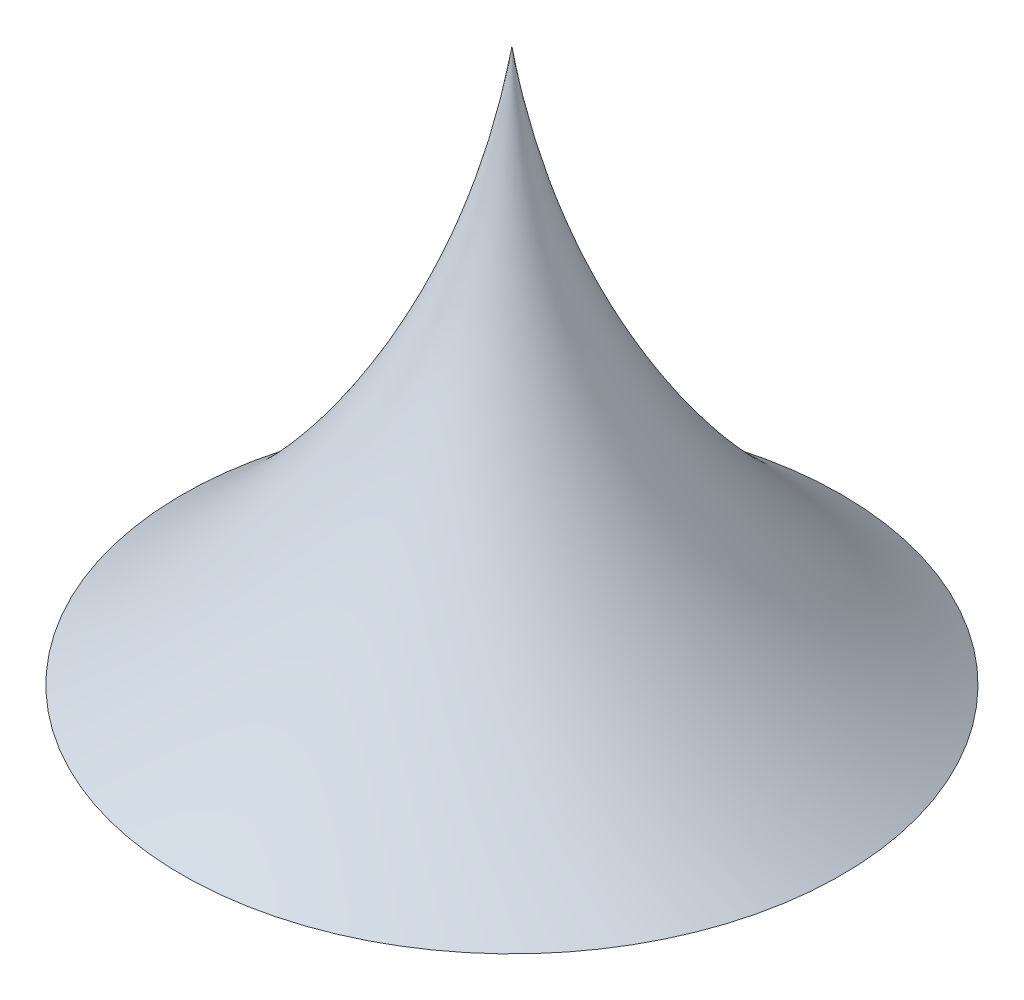
SolidWorks part; units mm, degrees
ref_plane "Front Plane" through (0, 0, 0) normal (0, 0, 1) x (1, 0, 0)
ref_plane "Top Plane" through (0, 0, 0) normal (0, 1, 0) x (1, 0, 0)
ref_plane "Right Plane" through (0, 0, 0) normal (1, 0, 0) x (0, 0, -1)
sketch "Sketch3" plane through (0, 0, 0) normal (0, 0, 1) x (1, 0, 0)
  line L0 (0, 0) -> (0, 60.7748)
  line L2 (52.9119, 0) -> (0, 0)
  arc A0 (0, 60.7748) -> (52.9119, 0) centre (74.1665, 71.9253) ccw
  dimension "D3" = 75
revolve "Revolve2" add sketch "Sketch3" angle 360 about L0
sketch "Sketch4" plane through (0, 0, 0) normal (1, 0, 0) x (0, 0, -1)
  line L1 (70.5048, 12) -> (-70.5048, 12)
  line L2 (70.5048, 12) -> (70.5048, 0)
  line L3 (70.5048, 0) -> (-70.5048, 0)
  line L4 (-70.5048, 12) -> (-70.5048, 0)
  point P4 (0, 0)
  dimension "D1" = 12
extrude "Cut-Extrude1" cut sketch "Sketch4" against normal through all and the other way through all
sketch "Sketch5" plane through (0, 12, 0) normal (0, -1, 0) x (1, 0, 0)
  line L1 (-5.4164, 4.9422) -> (-6.9883, -2.2197)
  line L2 (-6.9883, -2.2197) -> (-1.5719, -7.1619)
  line L3 (-1.5719, -7.1619) -> (5.4164, -4.9422)
  line L4 (5.4164, -4.9422) -> (6.9883, 2.2197)
  line L5 (6.9883, 2.2197) -> (1.5719, 7.1619)
  line L6 (1.5719, 7.1619) -> (-5.4164, 4.9422)
  circle A0 centre (0, 0) radius 6.35 construction
  dimension "D1" = 12.7
extrude "Cut-Extrude2" cut sketch "Sketch5" against normal blind 20
